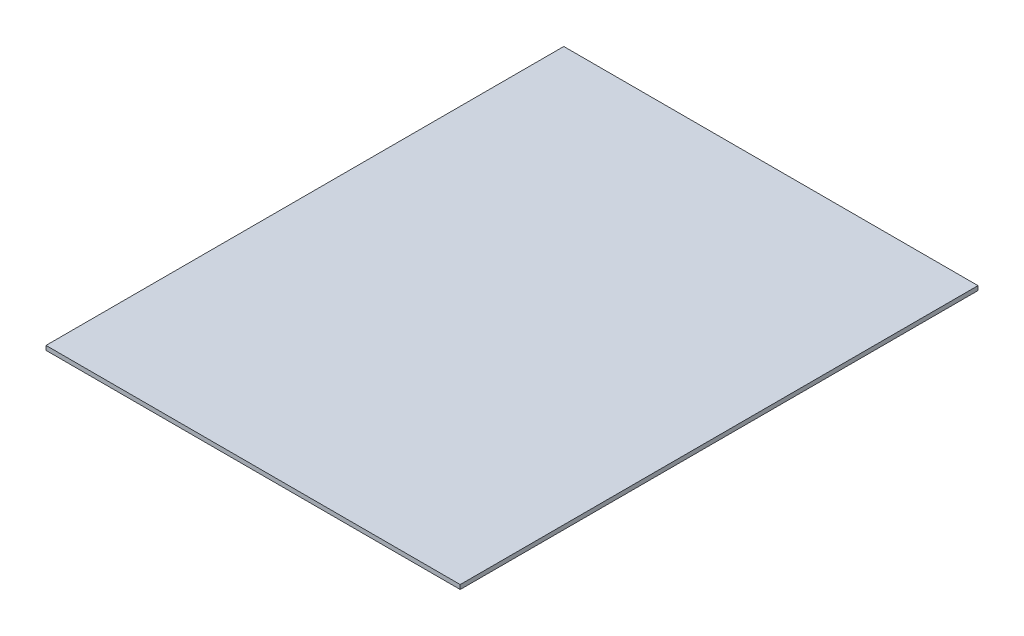
SolidWorks part; units mm, degrees
ref_plane "Front Plane" through (0, 0, 0) normal (0, 0, 1) x (1, 0, 0)
ref_plane "Top Plane" through (0, 0, 0) normal (0, 1, 0) x (1, 0, 0)
ref_plane "Right Plane" through (0, 0, 0) normal (1, 0, 0) x (0, 0, -1)
sketch "Sketch1" plane through (0, 0, 0) normal (0, 1, 0) x (1, 0, 0)
  line L1 (0, 0) -> (609.6, 0)
  line L2 (0, 0) -> (0, 762)
  line L3 (0, 762) -> (609.6, 762)
  line L4 (609.6, 0) -> (609.6, 762)
  dimension "D1" = 609.6
  dimension "D2" = 762
extrude "Boss-Extrude1" add sketch "Sketch1" along normal blind 6.35
